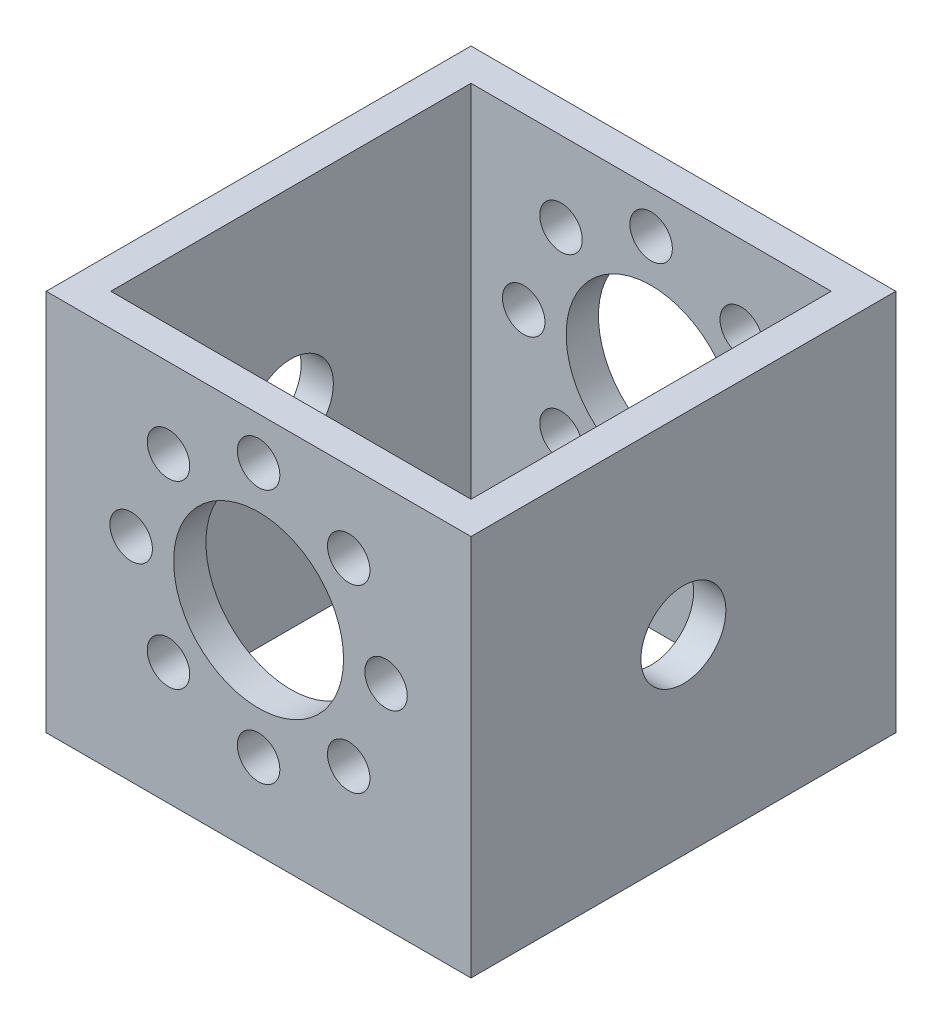
SolidWorks part; units mm, degrees
ref_plane "Front Plane" through (0, 0, 0) normal (0, 0, 1) x (1, 0, 0)
ref_plane "Top Plane" through (0, 0, 0) normal (0, 1, 0) x (1, 0, 0)
ref_plane "Right Plane" through (0, 0, 0) normal (1, 0, 0) x (0, 0, -1)
sketch "Sketch1" plane through (0, 0, 0) normal (0, 0, 1) x (1, 0, 0)
  line L0 (-31.75, 25.4) -> (31.75, 25.4)
  line L1 (-31.75, 25.4) -> (-31.75, -31.75)
  line L2 (-31.75, -31.75) -> (31.75, -31.75)
  line L3 (31.75, 25.4) -> (31.75, -31.75)
  line L4 (0, 25.4) -> (0, -31.75) construction
  line L5 (0, 0) -> (0, 19.05) construction
  circle A0 centre (0, 0) radius 12.7
  circle A2 centre (0, 0) radius 19.05 construction
  circle A3 centre (0, 19.05) radius 3.175
  circle A4 centre (13.4704, 13.4704) radius 3.175
  circle A5 centre (19.05, 0) radius 3.175
  circle A6 centre (13.4704, -13.4704) radius 3.175
  circle A7 centre (0, -19.05) radius 3.175
  circle A8 centre (-13.4704, -13.4704) radius 3.175
  circle A9 centre (-19.05, 0) radius 3.175
  circle A10 centre (-13.4704, 13.4704) radius 3.175
  point P2 (0, 25.4)
  dimension "D3" = 25.4
  dimension "D5" = 38.1
  dimension "D6" = 6.35
  dimension "D1" = 57.15
  dimension "D2" = 63.5
  dimension "D4" = 25.4
  dimension "D8" = 19.05
  dimension "D7" = 8
extrude "Boss-Extrude2" add sketch "Sketch1" along normal blind 4.826
sketch "Sketch2" plane through (31.75, 0, 0) normal (1, 0, 0) x (0, 0, -1)
  line L0 (-4.826, 25.4) -> (-58.674, 25.4)
  line L1 (-58.674, 25.4) -> (-58.674, -31.75)
  line L2 (-58.674, -31.75) -> (-4.826, -31.75)
  line L3 (-4.826, -31.75) -> (-4.826, 25.4)
  line L4 (-58.674, 25.4) -> (-4.826, -31.75) construction
  line L5 (-4.826, 25.4) -> (-58.674, -31.75) construction
  circle A0 centre (-31.75, -3.175) radius 6.35
  dimension "D2" = 12.7
  dimension "D1" = 53.848
extrude "Boss-Extrude3" add sketch "Sketch2" against normal blind 4.826
ref_plane "Plane1" through (0, 0, 0) normal (-1, 0, 0) x (0, 0, 1)
ref_plane "Plane2" through (0, 0, 31.75) normal (0, 0, 1) x (1, 0, 0)
mirror "Mirror1" about plane through (0, 0, 31.75) normal (0, 0, 1) of "Boss-Extrude2"
mirror "Mirror3" about plane through (0, 0, 0) normal (-1, 0, 0) of "Boss-Extrude3"
